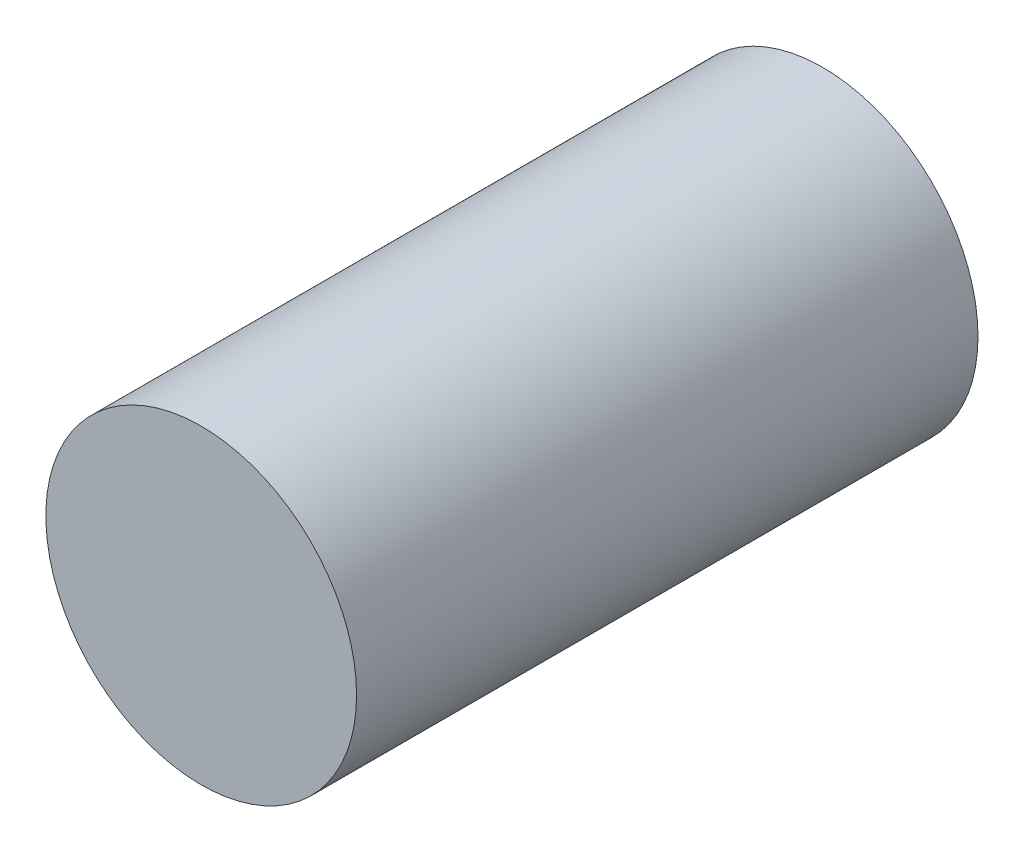
SolidWorks part; units mm, degrees
material "Rubber"
ref_plane "Front Plane" through (0, 0, 0) normal (0, 0, 1) x (1, 0, 0)
ref_plane "Top Plane" through (0, 0, 0) normal (0, 1, 0) x (1, 0, 0)
ref_plane "Right Plane" through (0, 0, 0) normal (1, 0, 0) x (0, 0, -1)
sketch "Sketch1" plane through (0, 0, 0) normal (0, 0, 1) x (1, 0, 0)
  circle A2 centre (475, -150) radius 7.5
  circle A3 centre (475, -150) radius 7.5
  dimension "D1" = 0
extrude "Boss-Extrude1" add sketch "Sketch1" along normal blind 30
